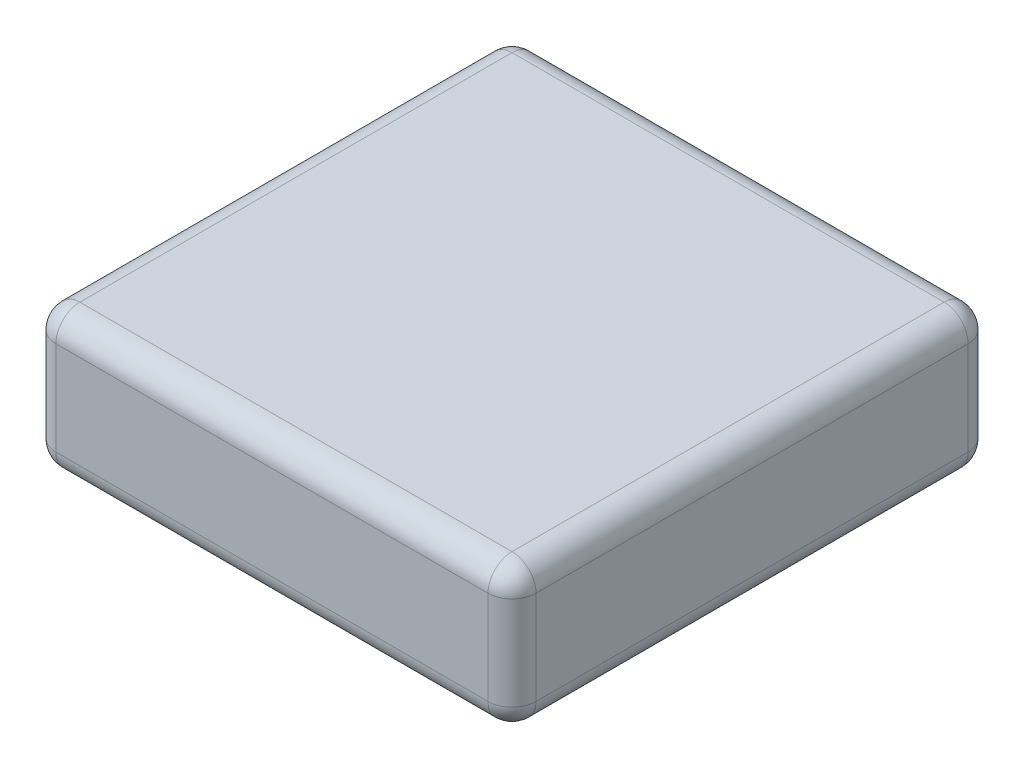
SolidWorks part; units mm, degrees
ref_plane "Front Plane" through (0, 0, 0) normal (0, 0, 1) x (1, 0, 0)
ref_plane "Top Plane" through (0, 0, 0) normal (0, 1, 0) x (1, 0, 0)
ref_plane "Right Plane" through (0, 0, 0) normal (1, 0, 0) x (0, 0, -1)
sketch "Sketch1" plane through (0, 0, 0) normal (0, 1, 0) x (1, 0, 0)
  line L1 (0, 0) -> (50.8, 0)
  line L2 (0, 0) -> (0, 50.8)
  line L3 (0, 50.8) -> (50.8, 50.8)
  line L4 (50.8, 0) -> (50.8, 50.8)
  dimension "D1" = 50.8
  dimension "D2" = 50.8
extrude "Boss-Extrude1" add sketch "Sketch1" along normal blind 15
fillet "Fillet1" radius 2.54 12 edges at (0, 15, -25.4) (0, 0, -25.4) (25.4, 15, -50.8) (0, 7.5, -50.8) (25.4, 0, -50.8) (50.8, 15, -25.4) (50.8, 7.5, -50.8) (50.8, 0, -25.4) (0, 7.5, 0) (25.4, 15, 0) (50.8, 7.5, 0) (25.4, 0, 0)
